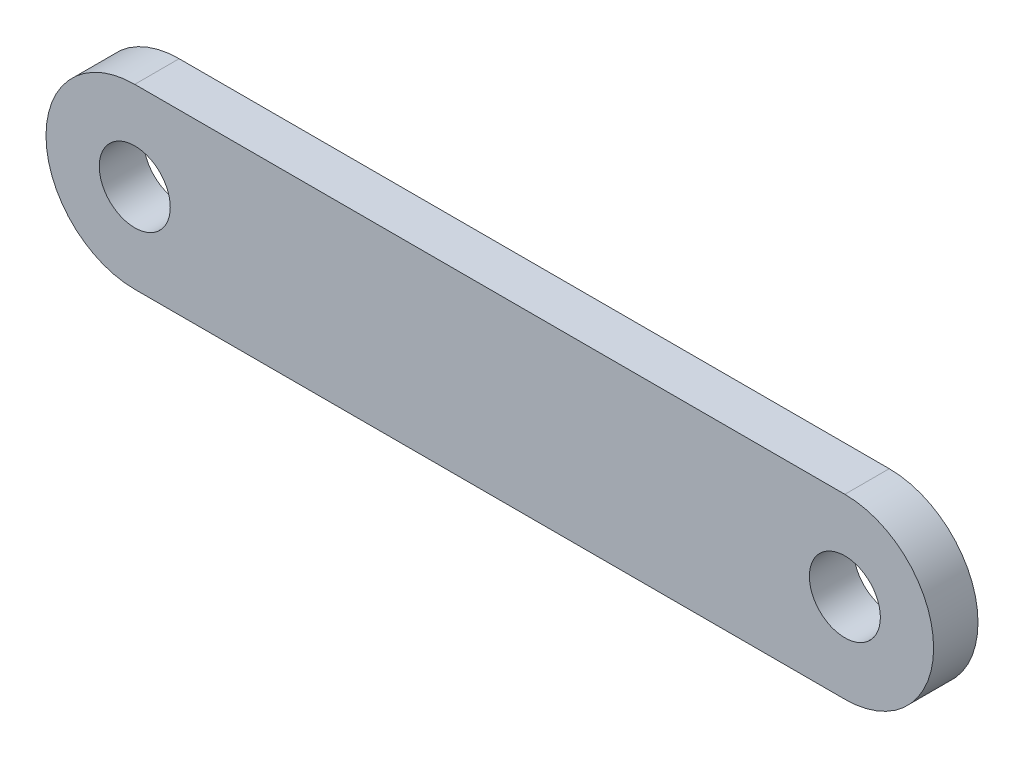
SolidWorks part; units mm, degrees
ref_plane "Front Plane" through (0, 0, 0) normal (0, 0, 1) x (1, 0, 0)
ref_plane "Top Plane" through (0, 0, 0) normal (0, 1, 0) x (1, 0, 0)
ref_plane "Right Plane" through (0, 0, 0) normal (1, 0, 0) x (0, 0, -1)
sketch "Sketch1" plane through (0, 0, 0) normal (0, 0, 1) x (1, 0, 0)
  line L1 (16, -2) -> (0, -2)
  line L2 (0, 2) -> (16, 2)
  arc A0 (0, 2) -> (0, -2) centre (0, 0) ccw
  arc A1 (16, -2) -> (16, 2) centre (16, 0) ccw
  circle A2 centre (0, 0) radius 0.8
  circle A3 centre (16, 0) radius 0.8
extrude "Boss-Extrude1" add sketch "Sketch1" along normal blind 1
